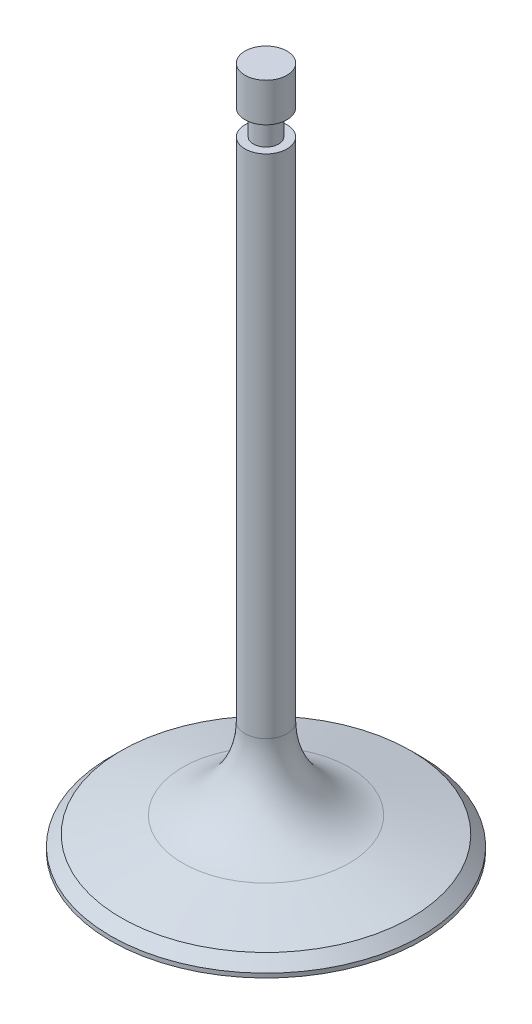
SolidWorks part; units mm, degrees
ref_plane "Front Plane" through (0, 0, 0) normal (0, 0, 1) x (1, 0, 0)
ref_plane "Top Plane" through (0, 0, 0) normal (0, 1, 0) x (1, 0, 0)
ref_plane "Right Plane" through (0, 0, 0) normal (1, 0, 0) x (0, 0, -1)
sketch "Sketch1" plane through (0, 0, 0) normal (1, 0, 0) x (0, 0, -1)
  line L0 (0, 0) -> (0, 82.79)
  line L1 (0, 82.79) -> (2.5, 82.79)
  line L2 (2.5, 82.79) -> (2.5, 78.19)
  line L3 (2.5, 78.19) -> (1.5, 78.19)
  line L4 (1.5, 78.19) -> (1.5, 75.19)
  line L5 (1.5, 75.19) -> (2.5, 75.19)
  line L6 (2.5, 75.19) -> (2.5, 14.8755)
  line L7 (9.9118, 5.2163) -> (17.25, 3.25)
  line L8 (17.25, 3.25) -> (18.5, 2)
  line L9 (18.5, 2) -> (18.5, 1.5)
  line L10 (0, 0) -> (-14.4169, 0) construction
  line L11 (18.5, 2) -> (3.2779, 2) construction
  arc A0 (2.5, 14.8755) -> (9.9118, 5.2163) centre (12.5, 14.8755) ccw
  arc A1 (18.5, 1.5) -> (0, 0) centre (0, 114.8333) cw
  dimension "D12" = 82.79
  dimension "D11" = 10
  dimension "D4" = 1.25
  dimension "D2" = 1.5
  dimension "D3" = 0.5
  dimension "D5" = 15
  dimension "D6" = 45
  dimension "D7" = 2.5
  dimension "D8" = 3
  dimension "D9" = 1
  dimension "D10" = 4.6
  dimension "D13" = 18.5
revolve "Revolve1" add sketch "Sketch1" angle 360 about L0
